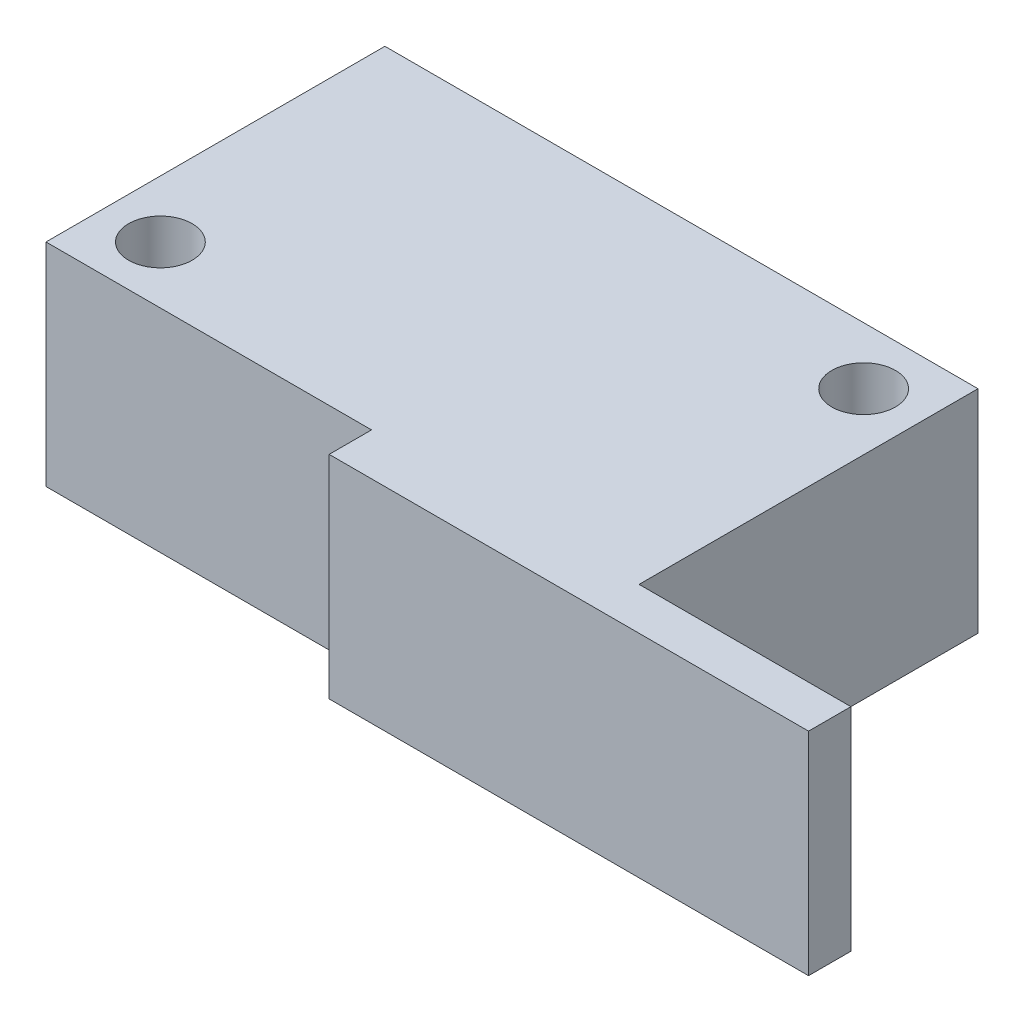
SolidWorks part; units mm, degrees
ref_plane "Front Plane" through (0, 0, 0) normal (0, 0, 1) x (1, 0, 0)
ref_plane "Top Plane" through (0, 0, 0) normal (0, 1, 0) x (1, 0, 0)
ref_plane "Right Plane" through (0, 0, 0) normal (1, 0, 0) x (0, 0, -1)
sketch "Sketch1" plane through (0, 0, 0) normal (0, 1, 0) x (1, 0, 0)
  line L1 (-14, 8) -> (14, 8)
  line L2 (-14, 8) -> (-14, -8)
  line L3 (-14, -8) -> (14, -8)
  line L4 (14, 8) -> (14, -8)
  line L5 (-14, 8) -> (14, -8) construction
  line L6 (-14, -8) -> (14, 8) construction
  point P0 (0, 0)
  dimension "D1" = 16
  dimension "D2" = 28
extrude "Boss-Extrude1" add sketch "Sketch1" along normal blind 10
sketch "Sketch2" plane through (0, 10, 0) normal (0, 1, 0) x (1, 0, 0)
  line L0 (14, 8) -> (-14, 8) construction
  line L2 (14, -8) -> (14, 8) construction
  line L3 (-14, 8) -> (-14, -8) construction
  line L4 (-14, -8) -> (14, -8) construction
  circle A0 centre (-11.3, -5.3) radius 1.5
  circle A1 centre (11.3, 5.3) radius 1.5
  dimension "D1" = 3
  dimension "D2" = 3
  dimension "D3" = 2.7
  dimension "D4" = 2.7
  dimension "D5" = 2.7
  dimension "D6" = 2.7
extrude "Cut-Extrude1" cut sketch "Sketch2" against normal up to next
sketch "Sketch3" plane through (0, 0, 8) normal (0, 0, 1) x (1, 0, 0)
  line L0 (-14, 10) -> (14, 10) construction
  line L1 (1.3682, 10) -> (24, 10)
  line L2 (1.3682, 10) -> (1.3682, 0)
  line L3 (1.3682, 0) -> (24, 0)
  line L4 (24, 10) -> (24, 0)
  line L5 (14, 10) -> (14, 0) construction
  dimension "D1" = 10
extrude "Boss-Extrude2" add sketch "Sketch3" along normal blind 2
